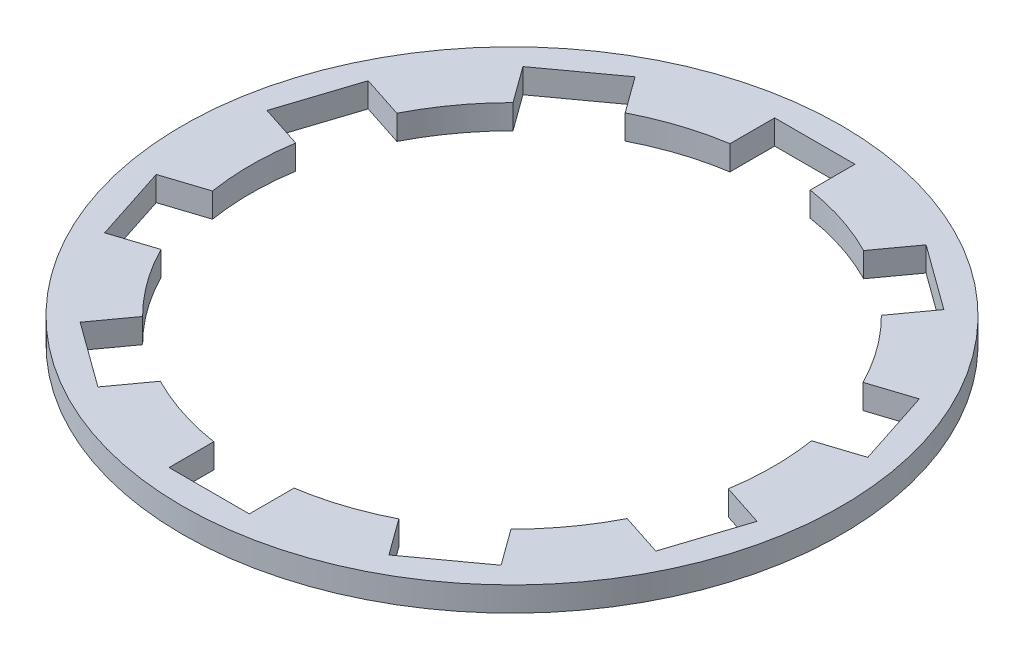
SolidWorks part; units mm, degrees
material "Plain Carbon Steel"
ref_plane "Front Plane" through (0, 0, 0) normal (0, 0, 1) x (1, 0, 0)
ref_plane "Top Plane" through (0, 0, 0) normal (0, 1, 0) x (1, 0, 0)
ref_plane "Right Plane" through (0, 0, 0) normal (1, 0, 0) x (0, 0, -1)
sketch "Sketch1" plane through (0, 0, 0) normal (0, 1, 0) x (1, 0, 0)
  circle A0 centre (0, 0) radius 7.5311
  circle A1 centre (0, 0) radius 5.969
  dimension "D1" = 15.0622
  dimension "D2" = 11.938
extrude "Boss-Extrude1" add sketch "Sketch1" along normal blind 0.5588
sketch "Sketch2" plane through (0, 0.5588, 0) normal (0, 1, 0) x (1, 0, 0)
  line L1 (0.9174, 5.0181) -> (-0.9174, 5.0181)
  line L2 (0.9174, 5.0181) -> (0.9174, 6.9199)
  line L3 (0.9174, 6.9199) -> (-0.9174, 6.9199)
  line L4 (-0.9174, 5.0181) -> (-0.9174, 6.9199)
  line L5 (0.9174, 5.0181) -> (-0.9174, 6.9199) construction
  line L6 (0.9174, 6.9199) -> (-0.9174, 5.0181) construction
  circle A0 centre (0, 0) radius 5.969 construction
  point P0 (0, 5.969)
extrude "Cut-Extrude1" cut sketch "Sketch2" against normal through all
pattern_circular "CirPattern1" count 10 over 360 about axis through (0, 0, 0) along (0, 1, 0) of "Cut-Extrude1"
